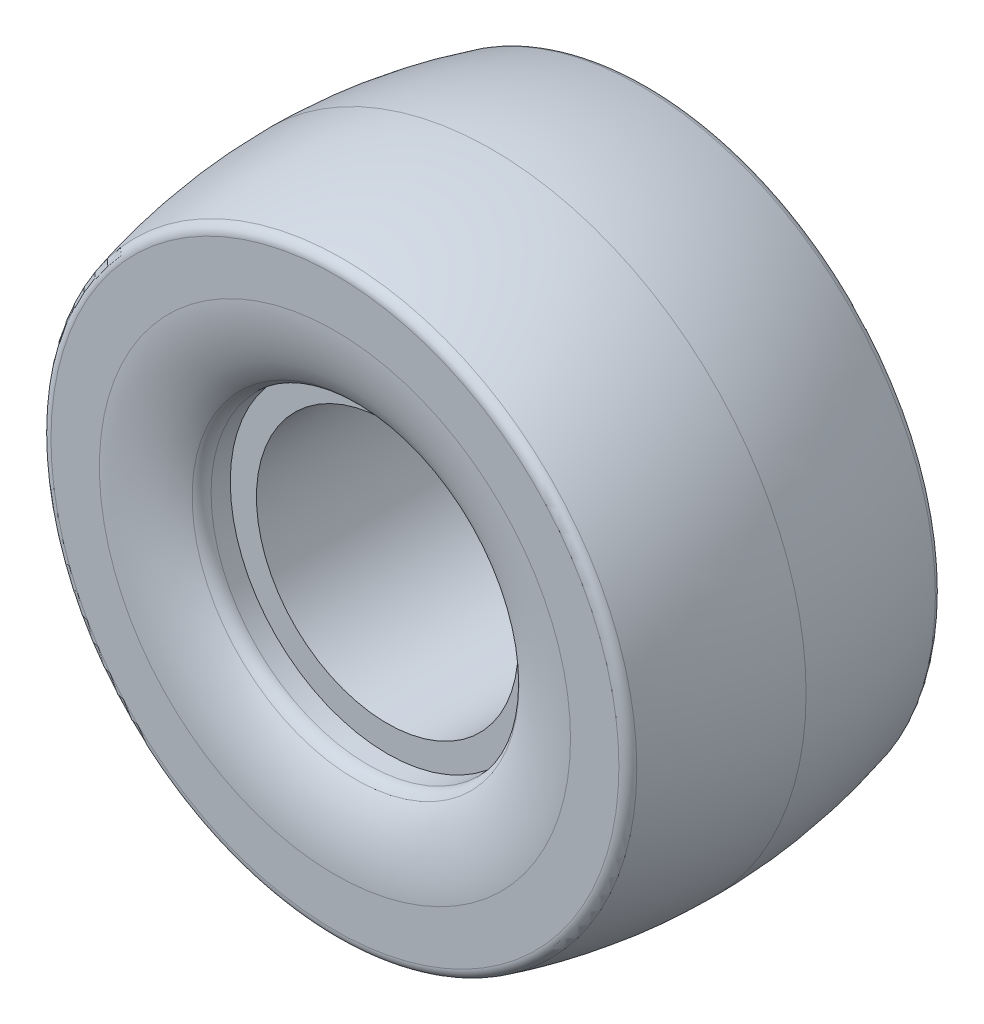
SolidWorks part; units mm, degrees
ref_plane "Front Plane" through (0, 0, 0) normal (0, 0, 1) x (1, 0, 0)
ref_plane "Top Plane" through (0, 0, 0) normal (0, 1, 0) x (1, 0, 0)
ref_plane "Right Plane" through (0, 0, 0) normal (1, 0, 0) x (0, 0, -1)
sketch "Sketch1" plane through (0, 0, 0) normal (1, 0, 0) x (0, 0, -1)
  line L0 (-30, 0) -> (30, 0) construction
  line L1 (0, 0) -> (0, 25) construction
  line L2 (0, 12.5) -> (-20, 12.5) construction
  line L3 (20, 25) -> (-20, 25)
  line L4 (-20, 25) -> (-20, 30)
  line L5 (-20, 30) -> (-23.6685, 30)
  line L6 (-30, 0) -> (-30, 30) construction
  line L7 (-30, 30) -> (-25, 30) construction
  line L8 (-30, 30) -> (-30, 60) construction
  line L9 (-30, 60) -> (0, 60) construction
  line L10 (-30, 38.6754) -> (-30, 51.3246) construction
  line L11 (20, 25) -> (20, 30)
  line L12 (20, 30) -> (23.6685, 30)
  line L13 (30, 54.2456) -> (30, 45)
  line L15 (-30, 60) -> (-33.1825, 60) construction
  line L16 (-33.1825, 60) -> (-33.1825, 55.7698) construction
  line L17 (-33.1825, 55.7698) -> (-30, 55.7698) construction
  line L18 (-33.1825, 55.7698) -> (-33.1825, 45) construction
  line L19 (-33.1825, 45) -> (-30, 45) construction
  line L20 (-30, 54.2456) -> (-30, 45)
  line L21 (0, 60) -> (0, 25) construction
  arc A0 (-30, 54.2456) -> (-28.5179, 56.1774) centre (-28, 54.2456) cw
  arc A1 (-23.6685, 30) -> (-26.0741, 31.2075) centre (-23.6685, 33) cw
  arc A2 (23.6685, 30) -> (26.0741, 31.2075) centre (23.6685, 33) ccw
  arc A3 (30, 54.2456) -> (28.5179, 56.1774) centre (28, 54.2456) ccw
  spline S0 degree 3 poles (-28.5179, 56.1774) (-23.7649, 57.4516) (-14.2589, 59.3629) (-4.753, 60) (0, 60) knots 0.024702 0.024702 0.024702 0.024702 0.262351 0.5 0.5 0.5 0.5
  spline S1 degree 3 poles (-30, 45) (-30, 42.6862) (-29.2604, 37.4316) (-27.2974, 32.8492) (-26.0741, 31.2075) knots 0 0 0 0 0.439021 0.878042 0.878042 0.878042 0.878042
  spline S2 degree 3 poles (30, 45) (30, 42.6862) (29.2604, 37.4316) (27.2974, 32.8492) (26.0741, 31.2075) knots 0 0 0 0 0.439021 0.878042 0.878042 0.878042 0.878042
  spline S3 degree 3 poles (28.5179, 56.1774) (23.7649, 57.4516) (14.2589, 59.3629) (4.753, 60) (0, 60) knots 0.024702 0.024702 0.024702 0.024702 0.262351 0.5 0.5 0.5 0.5
  point P14 (0, 0)
  point P15 (0, 0)
  point P24 (0, 0)
  dimension "D1" = 2
  dimension "D2" = 3
revolve "Revolve1" add sketch "Sketch1" angle 360 about L0
